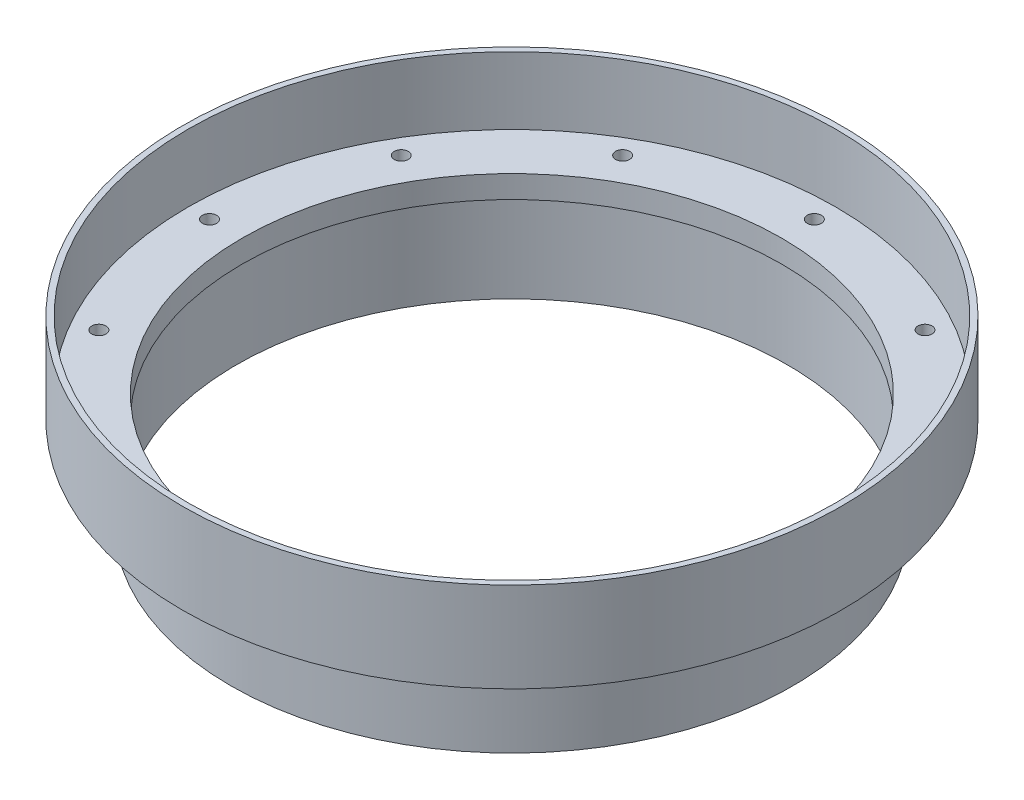
SolidWorks part; units mm, degrees
material "6061-T6 (SS)"
ref_plane "Front Plane" through (0, 0, 0) normal (0, 0, 1) x (1, 0, 0)
ref_plane "Top Plane" through (0, 0, 0) normal (0, 1, 0) x (1, 0, 0)
ref_plane "Right Plane" through (0, 0, 0) normal (1, 0, 0) x (0, 0, -1)
ref_axis "Axis1" through (0, 55, 0) along (0, -1, 0)
sketch "Cross Section" plane through (0, 0, 0) normal (0, 0, 1) x (1, 0, 0)
  line L0 (-38.1, 0) -> (-38.1, -3.175)
  line L1 (-38.1, -3.175) -> (-38.8874, -3.175)
  line L2 (-38.8874, -3.175) -> (-38.8874, -15.875)
  line L4 (0, -15.875) -> (-38.1, -15.875) construction
  line L5 (-39.6812, -15.875) -> (-39.6812, -3.175)
  line L6 (-39.6812, -3.175) -> (-46.5392, -3.175)
  line L7 (-46.5392, -3.175) -> (-46.5392, 9.525)
  line L8 (-46.5392, 9.525) -> (-45.72, 9.525)
  line L9 (-45.72, 9.525) -> (-45.72, 0)
  line L10 (-45.72, 0) -> (-38.1, 0)
  line L11 (-38.1, 0) -> (0, 0) construction
  line L12 (0, 55) -> (0, -55) construction
  line L13 (-38.8874, -15.875) -> (-39.6812, -15.875)
  line L14 (-45.72, 1.5875) -> (-45.72, 3.175) construction
  dimension "D1" = 0.7874
  dimension "D3" = 0.7937
  dimension "D5" = 6.858
  dimension "D6" = 12.7
  dimension "D9" = 3.175
  dimension "D8" = 38.1
revolve "Main" add sketch "Cross Section" angle 360 about axis through (0, 55, 0) along (0, -1, 0)
sketch "Hole Location" plane through (0, 0, 0) normal (0, 1, 0) x (1, 0, 0)
  line L0 (0, 0) -> (-42.7006, 0) construction
  circle A0 centre (0, 0) radius 42.7006 construction
  dimension "D1" = 85.4012
hole_wizard "#3-48 Tapped Hole1" positions "Sketch5" profile "Sketch7" tap size "#3-48" standard "ANSI Inch"
sketch "Sketch5" plane through (0, 0, 0) normal (0, 1, 0) x (1, 0, 0)
  point P0 (-42.7006, 0)
sketch "Sketch7" plane through (-42.7006, 0, 0) normal (1, 0, 0) x (0, 0, 1)
  line L0 (0, 0) -> (0, 3.901)
  line L1 (0, 3.901) -> (0.9969, 3.302)
  line L2 (0.9969, 3.302) -> (0.9969, 0)
  line L5 (0.9969, 0) -> (0, 0)
  line L10 (0, 3.901) -> (-0.997, 3.302) construction
  line L11 (0, -6.35) -> (0, 107.95) construction
  dimension "Tap Drill Dia." = 1.9939
  dimension "Tap Drill Depth" = 3.302
  dimension "Drill Angle" = 118
cosmetic thread "Hole Thread1" parameters "D1"=3.175, "D2"=2.5146
pattern_circular "Screw Holes" count 12 over 360 about axis through (0, 0, 0) along (0, 1, 0) of "#3-48 Tapped Hole1"
equation "\"D8@Cross Section\"=\"TANK DIAMETER@Cryo Tank.Assembly\"/2"
equation "\"D1@Hole Location\"=\"TANK DIAMETER@Cryo Tank.Assembly\"+\"GASKET SEAT THICKNESS@Cryo Tank.Assembly\"+\"LINER THICKNESS@Cryo Tank.Assembly\"+\"ALUMINUM LAP THICKNESS@Cryo Tank.Assembly\""
equation "\"D1@Cross Section\"=\"LINER THICKNESS@Cryo Tank.Assembly\""
equation "\"D3@Cross Section\"=\"ALUMINUM LAP THICKNESS@Cryo Tank.Assembly\""
equation "\"D5@Cross Section\"=2*\"CF THICKNESS@Cryo Tank.Assembly\"+\"NOMEX THICKNESS@Cryo Tank.Assembly\""
